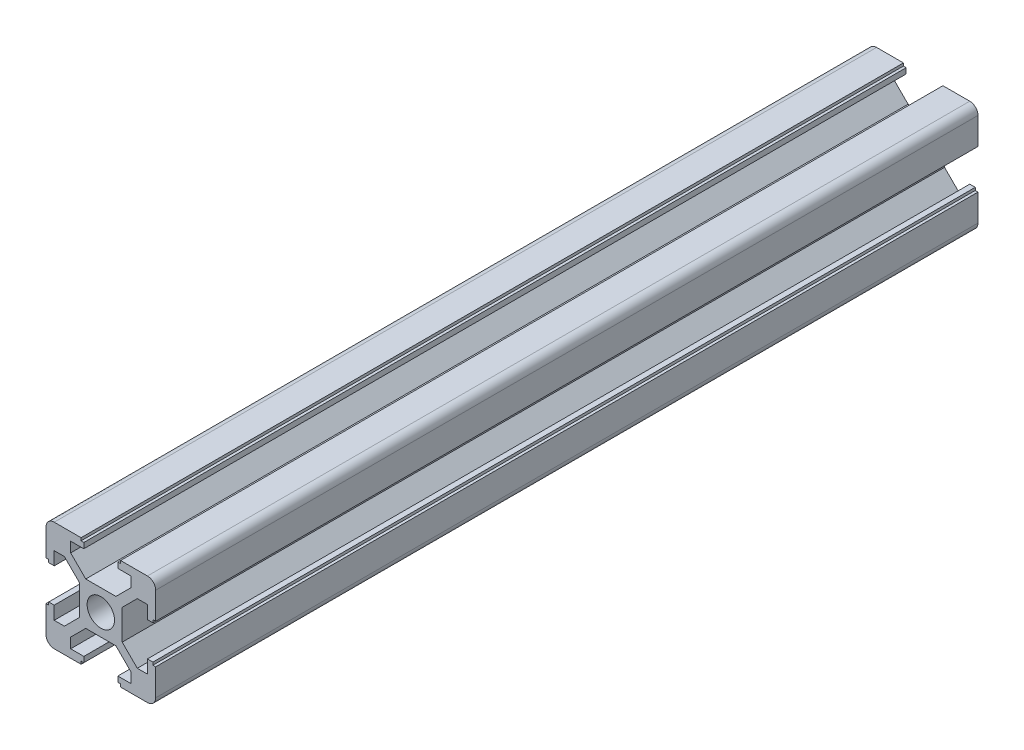
SolidWorks part; units mm, degrees
ref_plane "前视基准面" through (0, 0, 0) normal (0, 0, 1) x (1, 0, 0)
ref_plane "上视基准面" through (0, 0, 0) normal (0, 1, 0) x (1, 0, 0)
ref_plane "右视基准面" through (0, 0, 0) normal (1, 0, 0) x (0, 0, -1)
sketch "草图1" plane through (0, 0, 0) normal (0, 0, 1) x (1, 0, 0)
  line L0 (-3.6, 10) -> (-3.6, 9.5)
  line L1 (-3.6, 9.5) -> (-3.1, 9.5)
  line L2 (-3.1, 9.5) -> (-3.1, 8.5)
  line L3 (-3.1, 8.5) -> (-5.5, 8.5)
  line L4 (-8.5, -10) -> (-3.6, -10)
  line L5 (-10, -8.5) -> (-10, -3.6)
  line L6 (8.5, 10) -> (3.6, 10)
  line L7 (10, 8.5) -> (10, 3.6)
  line L8 (0, 14.8756) -> (0, 0) construction
  line L9 (0, 0) -> (14.1675, 0) construction
  line L10 (-5.5, 8.5) -> (-5.5, 6.65)
  line L11 (-5.5, 6.65) -> (-2.75, 3.9)
  line L12 (-2.75, 3.9) -> (2.75, 3.9)
  line L13 (5.5, 6.65) -> (2.75, 3.9)
  line L14 (5.5, 8.5) -> (5.5, 6.65)
  line L15 (3.1, 8.5) -> (5.5, 8.5)
  line L16 (3.1, 9.5) -> (3.1, 8.5)
  line L17 (3.6, 9.5) -> (3.1, 9.5)
  line L18 (3.6, 10) -> (3.6, 9.5)
  line L19 (-3.6, 10) -> (-8.5, 10)
  line L20 (10, 3.6) -> (9.5, 3.6)
  line L21 (9.5, 3.6) -> (9.5, 3.1)
  line L22 (9.5, 3.1) -> (8.5, 3.1)
  line L23 (8.5, 3.1) -> (8.5, 5.5)
  line L24 (8.5, 5.5) -> (6.65, 5.5)
  line L25 (6.65, 5.5) -> (3.9, 2.75)
  line L26 (3.9, 2.75) -> (3.9, -2.75)
  line L27 (6.65, -5.5) -> (3.9, -2.75)
  line L28 (8.5, -5.5) -> (6.65, -5.5)
  line L29 (8.5, -3.1) -> (8.5, -5.5)
  line L30 (9.5, -3.1) -> (8.5, -3.1)
  line L31 (9.5, -3.6) -> (9.5, -3.1)
  line L32 (10, -3.6) -> (9.5, -3.6)
  line L33 (3.6, -10) -> (3.6, -9.5)
  line L34 (3.6, -9.5) -> (3.1, -9.5)
  line L35 (3.1, -9.5) -> (3.1, -8.5)
  line L36 (3.1, -8.5) -> (5.5, -8.5)
  line L37 (5.5, -8.5) -> (5.5, -6.65)
  line L38 (5.5, -6.65) -> (2.75, -3.9)
  line L39 (2.75, -3.9) -> (-2.75, -3.9)
  line L40 (-5.5, -6.65) -> (-2.75, -3.9)
  line L41 (-5.5, -8.5) -> (-5.5, -6.65)
  line L42 (-3.1, -8.5) -> (-5.5, -8.5)
  line L43 (-3.1, -9.5) -> (-3.1, -8.5)
  line L44 (-3.6, -9.5) -> (-3.1, -9.5)
  line L45 (-3.6, -10) -> (-3.6, -9.5)
  line L46 (-10, -3.6) -> (-9.5, -3.6)
  line L47 (-9.5, -3.6) -> (-9.5, -3.1)
  line L48 (-9.5, -3.1) -> (-8.5, -3.1)
  line L49 (-8.5, -3.1) -> (-8.5, -5.5)
  line L50 (-8.5, -5.5) -> (-6.65, -5.5)
  line L51 (-6.65, -5.5) -> (-3.9, -2.75)
  line L52 (-3.9, -2.75) -> (-3.9, 2.75)
  line L53 (-6.65, 5.5) -> (-3.9, 2.75)
  line L54 (-8.5, 5.5) -> (-6.65, 5.5)
  line L55 (-8.5, 3.1) -> (-8.5, 5.5)
  line L56 (-9.5, 3.1) -> (-8.5, 3.1)
  line L57 (-9.5, 3.6) -> (-9.5, 3.1)
  line L58 (-10, 3.6) -> (-9.5, 3.6)
  line L59 (3.6, -10) -> (8.5, -10)
  line L60 (-10, 3.6) -> (-10, 8.5)
  line L61 (10, -3.6) -> (10, -8.5)
  circle A0 centre (0, 0) radius 2.5
  arc A1 (-10, 8.5) -> (-8.5, 10) centre (-8.5, 8.5) cw
  arc A2 (10, 8.5) -> (8.5, 10) centre (8.5, 8.5) ccw
  arc A3 (-8.5, -10) -> (-10, -8.5) centre (-8.5, -8.5) cw
  arc A4 (8.5, -10) -> (10, -8.5) centre (8.5, -8.5) ccw
  point P0 (-10, 0)
  point P1 (10, 0)
  point P2 (0, 10)
  point P3 (0, -10)
  point P4 (0, 0)
  point P5 (-10, -10)
  point P6 (10, -10)
  point P7 (10, 10)
  point P8 (-10, 10)
  point P13 (0, 0)
  dimension "D1" = 11
  dimension "D2" = 20
  dimension "D3" = 6.2
  dimension "D4" = 7.2
  dimension "D5" = 6.1
  dimension "D6" = 5
  dimension "D7" = 1.5
  dimension "D8" = 45
  dimension "D9" = 0.5
  dimension "D10" = 1
  dimension "D11" = 5.5
extrude "凸台-拉伸1" add sketch "草图1" along normal blind 150
